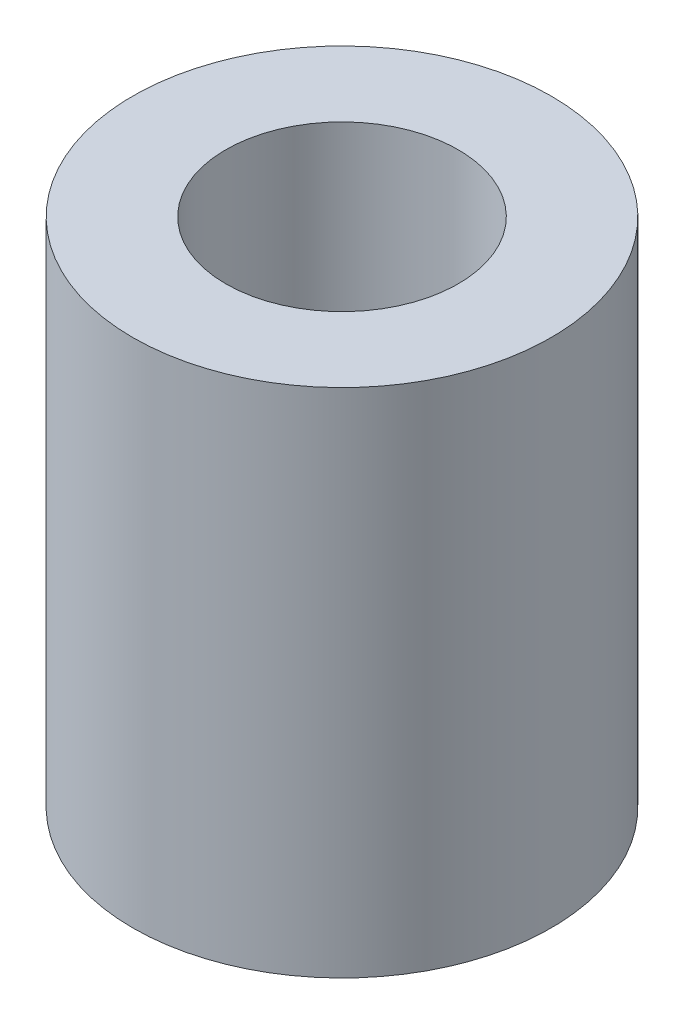
SolidWorks part; units mm, degrees
ref_plane "Front Plane" through (0, 0, 0) normal (0, 0, 1) x (1, 0, 0)
ref_plane "Top Plane" through (0, 0, 0) normal (0, 1, 0) x (1, 0, 0)
ref_plane "Right Plane" through (0, 0, 0) normal (1, 0, 0) x (0, 0, -1)
sketch "Sketch2" plane through (0, 0, 0) normal (0, 1, 0) x (1, 0, 0)
  circle A0 centre (0, 0) radius 2.7
  circle A1 centre (0, 0) radius 1.5
  dimension "D1" = 5.4
  dimension "D2" = 3
extrude "Boss-Extrude1" add sketch "Sketch2" along normal blind 6.6
